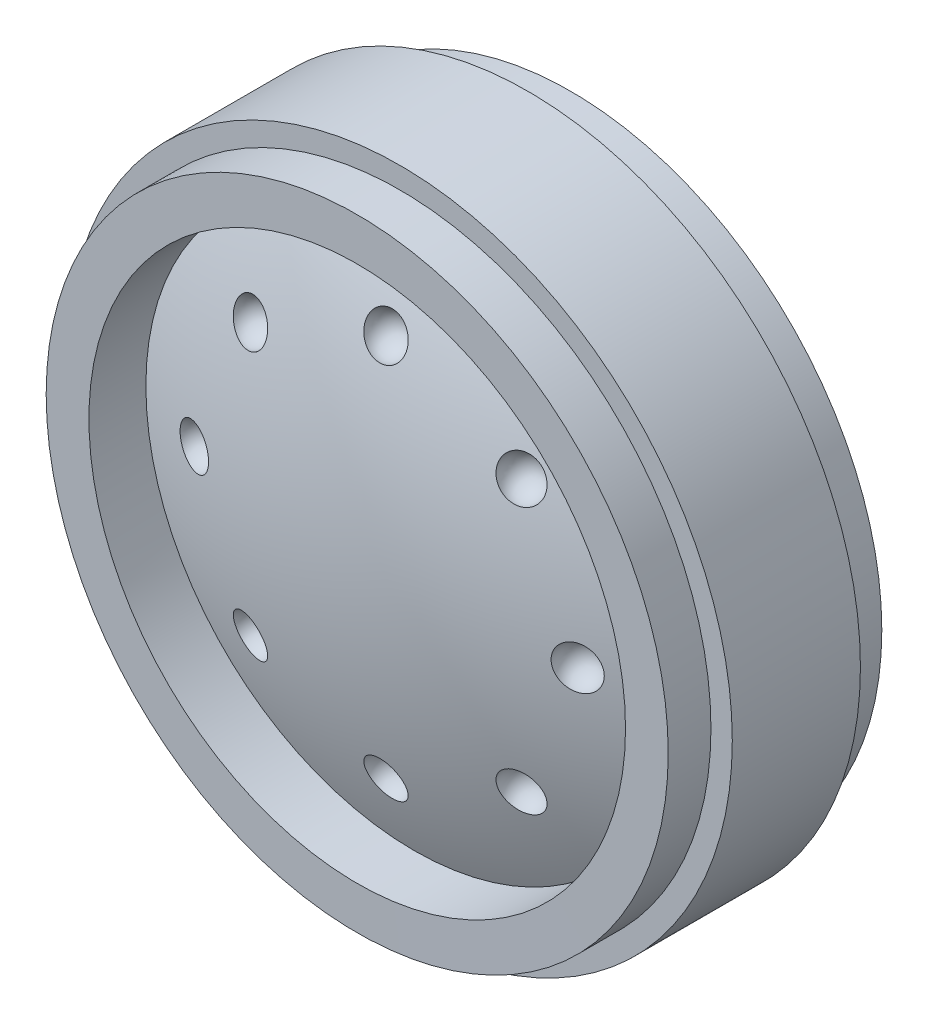
SolidWorks part; units mm, degrees
material "AISI 1035 Steel (SS)"
ref_plane "Front Plane" through (0, 0, 0) normal (0, 0, 1) x (1, 0, 0)
ref_plane "Top Plane" through (0, 0, 0) normal (0, 1, 0) x (1, 0, 0)
ref_plane "Right Plane" through (0, 0, 0) normal (1, 0, 0) x (0, 0, -1)
sketch "Sketch1" plane through (0, 0, 0) normal (1, 0, 0) x (0, 0, -1)
  line L0 (-6.049, 0) -> (-0.0013, 0)
  line L2 (-3.6297, 18.829) -> (3.6297, 18.829)
  line L3 (-6.049, 15.1994) -> (-2.823, 15.1994)
  line L4 (3.6297, 17.62) -> (6.0503, 17.62)
  line L5 (3.6297, 18.829) -> (3.6297, 17.62)
  line L6 (6.0503, 17.62) -> (6.049, 15.1994)
  line L7 (6.049, 15.1994) -> (2.823, 15.1994)
  line L8 (-6.0503, 17.62) -> (-6.049, 15.1994)
  line L9 (-3.6297, 18.829) -> (-3.6297, 17.62)
  line L10 (-3.6297, 17.62) -> (-6.0503, 17.62)
  line L12 (-0.0013, 0) -> (-0.0013, 3.2304)
  line L14 (5.9093, 3.2304) -> (-0.0013, 3.2304)
  arc A0 (5.9093, 3.2304) -> (2.823, 15.1994) centre (-31.3703, 0) ccw
  arc A1 (-6.049, 0) -> (-2.823, 15.1994) centre (31.3703, 0) cw
revolve "Revolve1" add sketch "Sketch1" angle 360 about L0
ref_plane "Plane1" through (0, 0, 4.4361) normal (0, 0, 1) x (1, 0, 0)
sketch "Sketch2" plane through (0, 0, 4.4361) normal (0, 0, 1) x (1, 0, 0)
  line L0 (-1.209, 10.8636) -> (1.209, 10.8636)
  arc A0 (1.209, 10.8636) -> (-1.209, 10.8636) centre (0, 10.8636) ccw
  dimension "D1" = 10.8636
  dimension "D2" = 0
revolve "Cut-Revolve1" cut sketch "Sketch2" angle 360 about L0
pattern_circular "CirPattern1" count 8 every 45 about axis through (0, 0, 0) along (0, 0, 1) of "Cut-Revolve1"
mirror "Mirror1" about plane through (0, 0, 0) normal (0, 0, 1) of "CirPattern1", "Cut-Revolve1"
